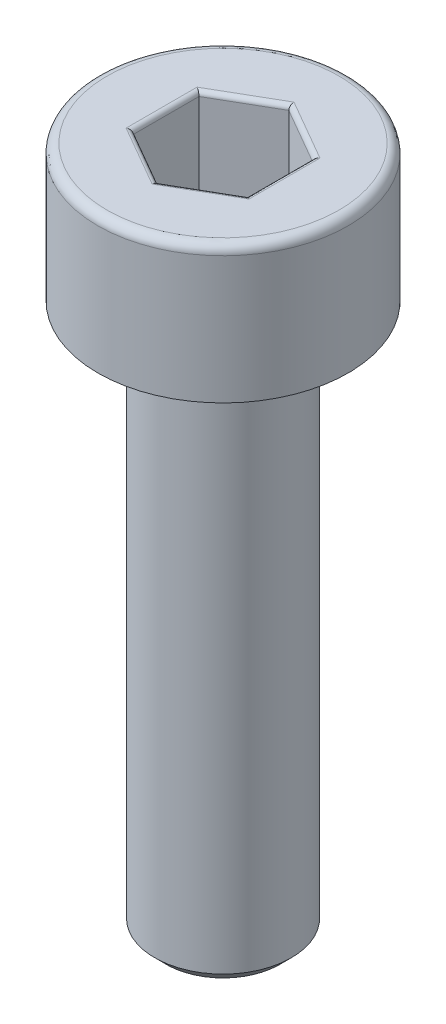
SolidWorks part; units mm, degrees
ref_plane "Front Plane" through (0, 0, 0) normal (0, 0, 1) x (1, 0, 0)
ref_plane "Top Plane" through (0, 0, 0) normal (0, 1, 0) x (1, 0, 0)
ref_plane "Right Plane" through (0, 0, 0) normal (1, 0, 0) x (0, 0, -1)
sketch "Sketch1" plane through (0, 0, 0) normal (0, 0, 1) x (1, 0, 0)
  line L0 (0, 0) -> (0, -47.0967) construction
  line L1 (0, -15) -> (-1.5, -15)
  line L2 (-1.5, -15) -> (-1.5, -3)
  line L3 (-1.5, -3) -> (-2.75, -3)
  line L4 (-2.75, -3) -> (-2.75, 0)
  line L5 (-2.75, 0) -> (0, 0)
  line L6 (0, 0) -> (0, -15)
  dimension "D1" = 12
  dimension "d" = 3
  dimension "k" = 3
  dimension "dk" = 5.5
revolve "Revolve1" add sketch "Sketch1" angle 360 about L0
chamfer "Chamfer1" distance 0.25 angle 45 2 edges at (0, -3, 1.5) (0, -15, 1.5)
fillet "Fillet1" radius 0.2 1 edges at (0, 0, 2.75)
sketch "Sketch2" plane through (0, 0, 0) normal (0, 1, 0) x (1, 0, 0)
  line L1 (0, 1.4434) -> (-1.25, 0.7217)
  line L2 (-1.25, 0.7217) -> (-1.25, -0.7217)
  line L3 (-1.25, -0.7217) -> (0, -1.4434)
  line L4 (0, -1.4434) -> (1.25, -0.7217)
  line L5 (1.25, -0.7217) -> (1.25, 0.7217)
  line L6 (1.25, 0.7217) -> (0, 1.4434)
  circle A0 centre (0, 0) radius 1.25 construction
  dimension "s" = 2.5
extrude "Cut-Extrude1" cut sketch "Sketch2" against normal blind 2
fillet "Fillet2" radius 0.1 12 edges at (-0.625, 0, -1.0825) (-1.25, 0, 0) (-0.625, 0, 1.0825) (0.625, 0, 1.0825) (1.25, 0, 0) (0.625, 0, -1.0825) (1.25, -2, 0) (0.625, -2, 1.0825) (-0.625, -2, 1.0825) (-1.25, -2, 0) (-0.625, -2, -1.0825) (0.625, -2, -1.0825)
